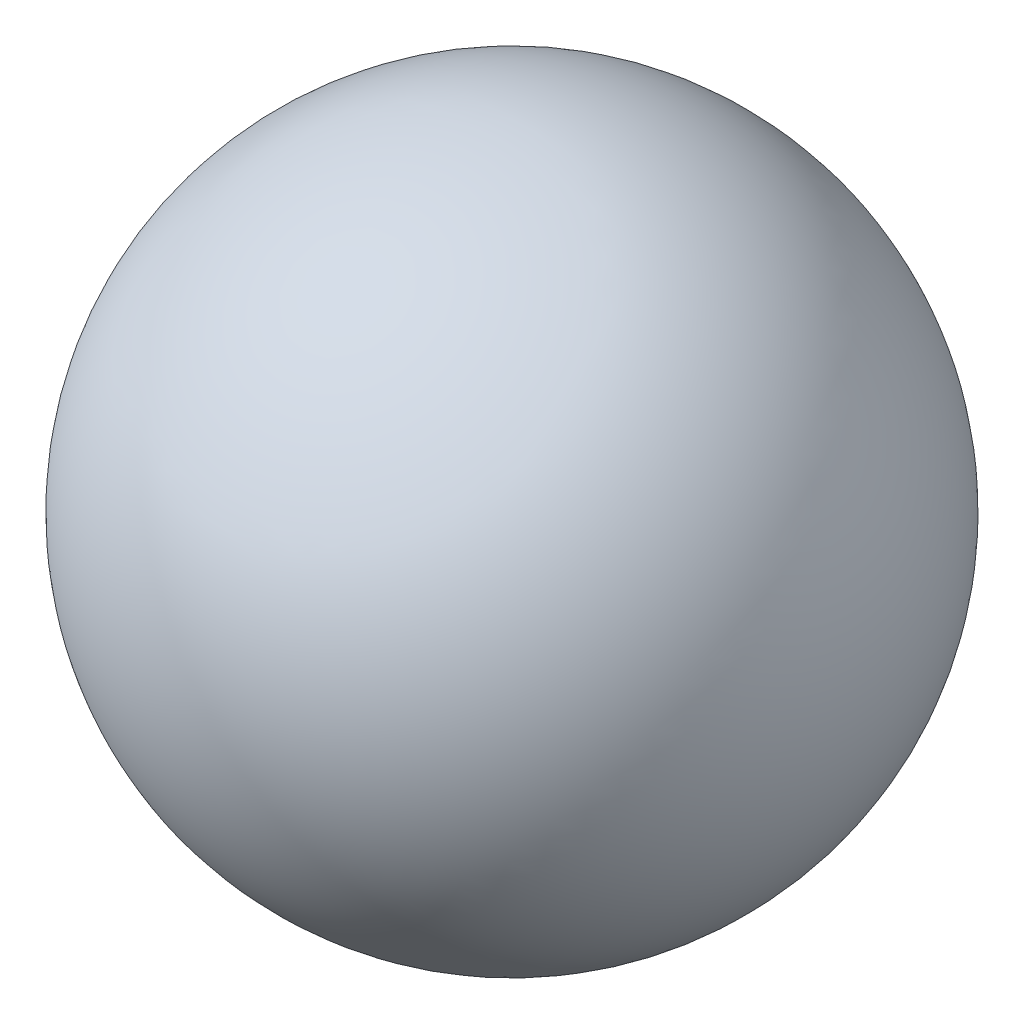
SolidWorks part; units mm, degrees
ref_plane "Front Plane" through (0, 0, 0) normal (0, 0, 1) x (1, 0, 0)
ref_plane "Top Plane" through (0, 0, 0) normal (0, 1, 0) x (1, 0, 0)
ref_plane "Right Plane" through (0, 0, 0) normal (1, 0, 0) x (0, 0, -1)
sketch "Sketch1" plane through (0, 0, 0) normal (0, 0, 1) x (1, 0, 0)
sketch "Sketch2" plane through (0, 0, 0) normal (0, 1, 0) x (1, 0, 0)
  line L0 (0, 7.5) -> (0, -7.5) construction
  line L1 (0, 7.5) -> (0, -7.5)
  arc A0 (0, -7.5) -> (0, 7.5) centre (0, 0) ccw
revolve "Revolve1" add sketch "Sketch2" angle 360 about L0
